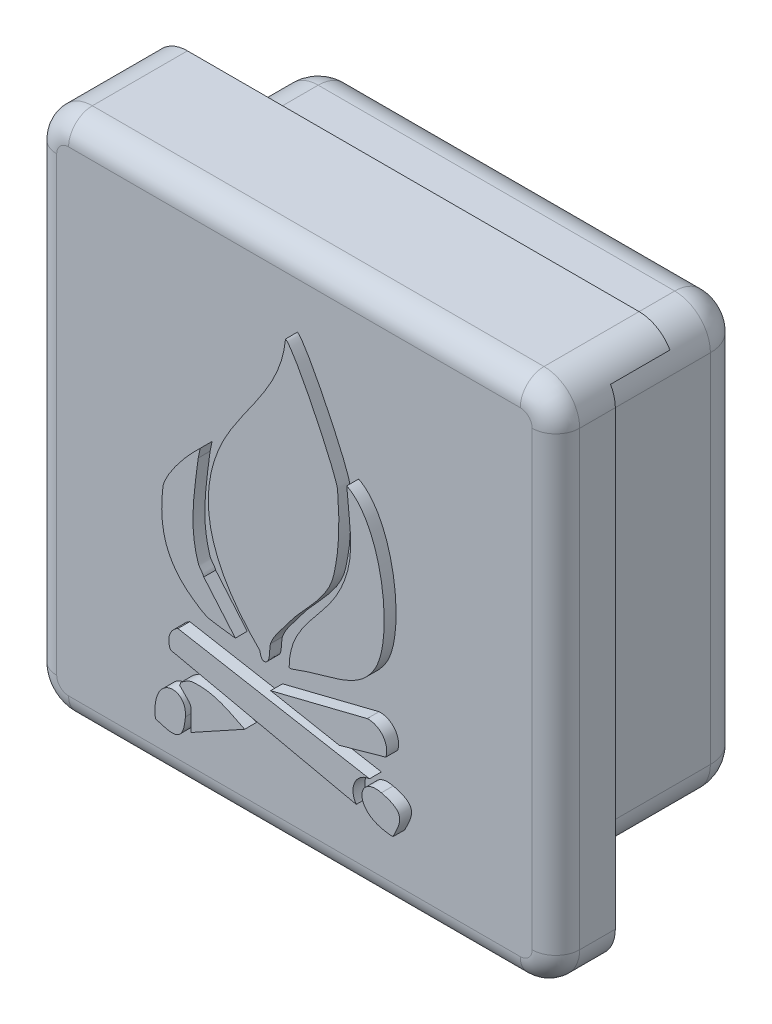
SolidWorks part; units mm, degrees
ref_plane "Plan de face" through (0, 0, 0) normal (0, 0, 1) x (1, 0, 0)
ref_plane "Plan de dessus" through (0, 0, 0) normal (0, 1, 0) x (1, 0, 0)
ref_plane "Plan de droite" through (0, 0, 0) normal (1, 0, 0) x (0, 0, -1)
sketch "Esquisse2" plane through (0, 0, 0) normal (0, 0, 1) x (1, 0, 0)
  line L1 (0, 0) -> (44, 0)
  line L2 (0, 0) -> (0, 44)
  line L3 (0, 44) -> (44, 44)
  line L4 (44, 0) -> (44, 44)
  dimension "D1" = 44
extrude "Boss.-Extru.1" add sketch "Esquisse2" along normal blind 10
sketch "Esquisse3" plane through (0, 0, 0) normal (0, 0, -1) x (-1, 0, 0)
  line L0 (-44, 44) -> (0, 44) construction
  line L1 (-40, 4) -> (-4, 4)
  line L2 (-40, 4) -> (-40, 40)
  line L3 (-40, 40) -> (-4, 40)
  line L4 (-4, 4) -> (-4, 40)
  line L5 (0, 44) -> (0, 0) construction
  dimension "D1" = 36
  dimension "D2" = 36
  dimension "D3" = 4
  dimension "D4" = 4
extrude "Boss.-Extru.2" add sketch "Esquisse3" along normal blind 10
sketch "Esquisse4" plane through (0, 0, 0) normal (0, 0, -1) x (-1, 0, 0)
  line L0 (-40, 40) -> (-4, 40)
  line L1 (-4, 40) -> (-4, 4)
  line L2 (-4, 4) -> (-40, 4)
  line L3 (-40, 4) -> (-40, 40)
  line L4 (-44, 42.5) -> (-1.5, 42.5)
  line L5 (-44, 0) -> (-44, 44) construction
  line L6 (-1.5, 42.5) -> (-1.5, 0)
  line L7 (0, 0) -> (-44, 0) construction
  line L8 (-1.5, 0) -> (-44, 0)
  line L9 (-44, 0) -> (-44, 42.5)
  line L10 (-44, 44) -> (0, 44) construction
  dimension "D1" = 1.5
  dimension "D2" = 2.5
extrude "Enlèv. mat.-Extru.1" cut sketch "Esquisse4" against normal blind 5
fillet "Congé1" radius 3 13 edges at (22, 40, -10) (4, 22, -10) (22, 4, -10) (40, 22, -10) (44, 0, 7.5) (44, 44, 5) (0, 0, 5) (0, 44, 5) (1.5, 42.5, 2.5) (4, 4, -2.5) (4, 40, -2.5) (40, 4, -2.5) (40, 40, -2.5)
fillet "Congé2" radius 2 8 edges at (0.8787, 0.8787, 10) (0, 22, 10) (0.8787, 43.1213, 10) (22, 44, 10) (43.1213, 43.1213, 10) (44, 22, 10) (43.1213, 0.8787, 10) (22, 0, 10)
sketch "Esquisse7" plane through (0, 0, 10) normal (0, 0, 1) x (1, 0, 0)
  line L0 (15.3741, 17.3468) -> (18.0303, 14.2218)
  line L1 (30.6866, 11.8781) -> (26.7803, 10.7843)
  line L2 (26.7803, 10.7843) -> (20.9991, 11.8781)
  line L3 (20.9991, 11.8781) -> (29.1241, 13.9093)
  line L4 (18.8116, 7.9718) -> (14.2803, 5.4718)
  line L5 (13.2006, 12.5063) -> (29.3172, 9.6184)
  line L7 (28.2006, 7.1938) -> (12.5756, 10.6313)
  line L9 (14.4366, 25.9406) -> (15.0694, 26.5734)
  line L10 (15.0694, 26.5734) -> (14.9053, 25.7843)
  arc A0 (29.1241, 13.9093) -> (30.6866, 11.8781) centre (29.2193, 12.366) cw
  arc A2 (12.5756, 10.6313) -> (13.2006, 12.5063) centre (13.8256, 11.2563) cw
  arc A3 (29.3172, 9.6184) -> (28.2006, 7.1938) centre (29.4761, 8.0758) ccw
  spline S0 degree 3 poles (14.9053, 25.7843) (14.5904, 23.2651) (14.0913, 20.5702) (14.9053, 18.1281) (15.0014, 17.84) (15.2781, 17.635) (15.3741, 17.3468) knots 0 0 0 0 1 1 1 2 2 2 2
  spline S1 degree 3 poles (18.0303, 14.2218) (17.3012, 14.326) (16.5651, 14.3899) (15.8428, 14.5343) (15.423, 14.6183) (14.8381, 15.0288) (14.4366, 15.3156) (12.0497, 17.0205) (11.5958, 19.2938) (11.9366, 22.1906) (12.0542, 23.1898) (13.6924, 25.1964) (14.4366, 25.9406) knots 0 0 0 0 1 1 1 2 2 2 3 3 3 4 4 4 4
  spline S2 degree 3 poles (20.9991, 15.3156) (20.8271, 14.7997) (21.0462, 13.925) (20.5303, 13.7531) (20.1531, 13.6274) (20.1379, 14.3018) (20.0616, 14.3781) (16.5677, 17.872) (14.6135, 21.9332) (16.4678, 26.8781) (17.9717, 30.8884) (21.8464, 33.6987) (22.2491, 38.1281) knots 4 4 4 4 5 5 5 6 6 6 7 7 7 8 8 8 8
  spline S3 degree 3 poles (22.2491, 38.1281) (23.0247, 37.7403) (26.55, 30.317) (26.6241, 29.3781) (26.8247, 26.8369) (26.7937, 25.1415) (26.3116, 22.9718) (25.8437, 20.8661) (23.7633, 19.3417) (22.5616, 17.6593) (22.0936, 17.0042) (21.2572, 16.0898) (20.9991, 15.3156) knots 0 0 0 0 1 1 1 2 2 2 3 3 3 4 4 4 4
  spline S4 degree 3 poles (22.8741, 14.3781) (22.7769, 14.3407) (22.5616, 14.2739) (22.5616, 14.3781) (22.5616, 17.7246) (25.3852, 19.244) (26.7803, 22.0343) (28.2695, 25.0127) (27.6271, 26.8984) (27.4053, 30.0031) knots 3 3 3 3 4 4 4 5 5 5 6 6 6 6
  spline S5 degree 3 poles (27.4053, 30.0031) (30.4392, 28.4861) (31.4108, 20.5851) (29.7491, 17.8156) (28.5783, 15.8642) (26.7183, 15.5866) (24.7491, 15.0031) (24.1174, 14.8159) (23.489, 14.6146) (22.8741, 14.3781) knots 0 0 0 0 1 1 1 2 2 2 3 3 3 3
  spline S6 degree 3 poles (13.8256, 6.3836) (13.6649, 4.2944) (12.8351, 4.4911) (11.3077, 4.9834) knots 1 1 1 1 2 2 2 2
  spline S7 degree 3 poles (11.3077, 4.9834) (10.8882, 8.4435) (13.9957, 8.5946) (13.8256, 6.3836) knots 0 0 0 0 1 1 1 1
  spline S8 degree 3 poles (13.3428, 8.4406) (13.3949, 8.5448) (13.4043, 8.6854) (13.4991, 8.7531) (13.7834, 8.9562) (14.0891, 9.1853) (14.4366, 9.2218) (16.1347, 9.4006) (17.3848, 8.6852) (18.8116, 7.9718) knots 0 0 0 0 1 1 1 2 2 2 3 3 3 3
  spline S9 degree 3 poles (14.2803, 5.4718) (14.2803, 7.7728) (14.5937, 7.1897) (13.3428, 8.4406) knots 0 0 0 0 1 1 1 1
  spline S10 degree 3 poles (30.313, 9.0938) (32.3492, 8.5995) (32.0217, 7.8121) (31.2904, 6.3836) knots 1 1 1 1 2 2 2 2
  spline S11 degree 3 poles (31.2904, 6.3836) (27.8079, 6.5256) (28.158, 9.6169) (30.313, 9.0938) knots 0 0 0 0 1 1 1 1
extrude "Boss.-Extru.4" add sketch "Esquisse7" along normal blind 1
